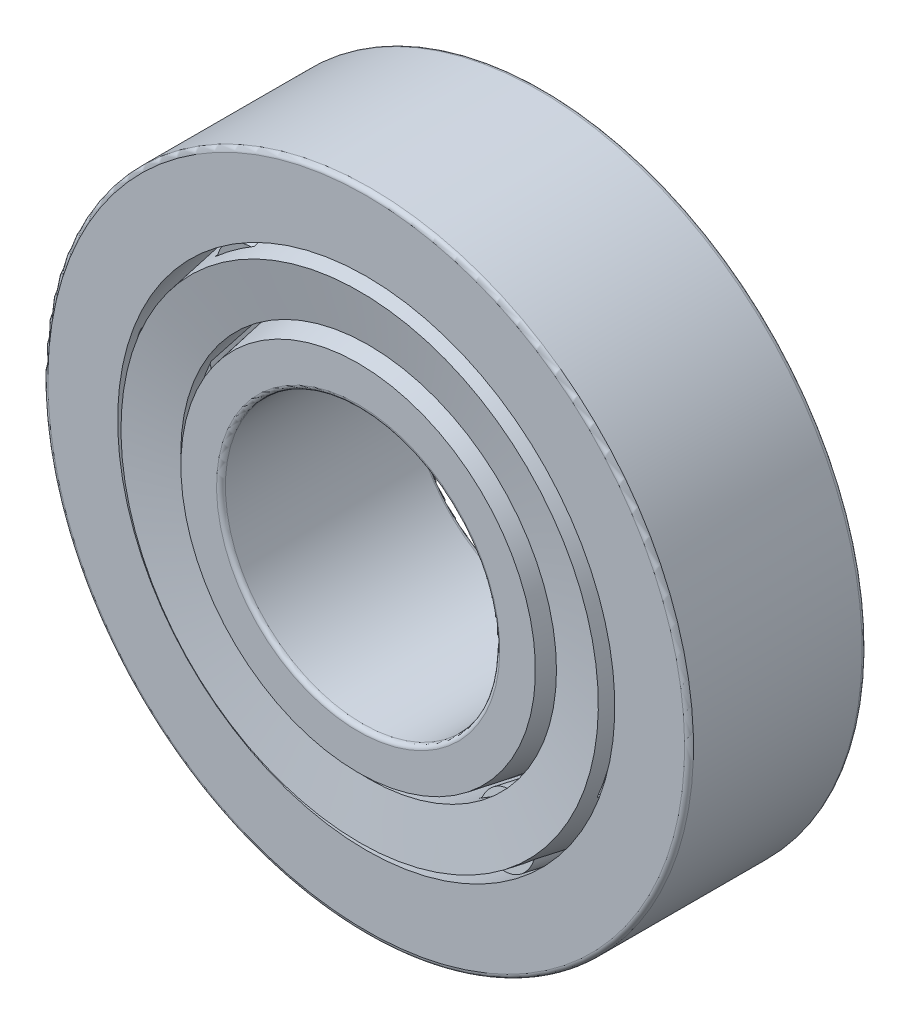
SolidWorks part; units mm, degrees
ref_plane "Front Plane" through (0, 0, 0) normal (0, 0, 1) x (1, 0, 0)
ref_plane "Top Plane" through (0, 0, 0) normal (0, 1, 0) x (1, 0, 0)
ref_plane "Right Plane" through (0, 0, 0) normal (1, 0, 0) x (0, 0, -1)
sketch "Sketch1" plane through (0, 0, 0) normal (1, 0, 0) x (0, 0, -1)
  line L0 (-6, 0) -> (6, 0) construction
  line L1 (0, 0) -> (0, 20) construction
  line L2 (-6, 8.5) -> (6, 8.5) construction
  line L3 (6, 8.5) -> (6, 13.1) construction
  line L4 (6, 13.1) -> (-6, 10.9841) construction
  line L5 (-6, 10.9841) -> (-6, 8.5) construction
  line L7 (-5.5, 20) -> (5.5, 20)
  line L8 (5.5, 20) -> (5.5, 17.3396)
  line L9 (5.5, 17.3396) -> (-5.5, 15.4)
  line L10 (-5.5, 15.4) -> (-5.5, 20)
  line L12 (6.5099, 17.5177) -> (7.25, 13.3204) construction
  line L13 (-5.2599, 11.1146) -> (-6, 15.3118) construction
  line L14 (-6, 10.9841) -> (-5.2599, 11.1146) construction
  line L15 (-6, 10.9841) -> (7.25, 13.3204) construction
  line L20 (-6, -10.9841) -> (7.25, -13.3204) construction
  line L21 (-6, -10.9841) -> (-5.2599, -11.1146) construction
  line L22 (-5.2599, -11.1146) -> (-6, -15.3118) construction
  line L23 (6.5099, -17.5177) -> (7.25, -13.3204) construction
  line L24 (-6, -10.9841) -> (-6, -8.5) construction
  line L25 (6, -13.1) -> (-6, -10.9841) construction
  line L26 (6, -8.5) -> (6, -13.1) construction
  line L27 (-6, -8.5) -> (6, -8.5) construction
  line L28 (-5.5, -15.4) -> (-5.5, -20) construction
  line L29 (5.5, -17.3396) -> (-5.5, -15.4) construction
  line L30 (5.5, -20) -> (5.5, -17.3396) construction
  line L31 (-5.5, -20) -> (5.5, -20) construction
  point P5 (0, 8.5)
  point P37 (0, -8.5)
  dimension "Width" = 12
  dimension "OD" = 40
  dimension "Shaft Dia" = 17
  dimension "D1" = 100
  dimension "D2" = 11.5
  dimension "D3" = 4.6
  dimension "Outer Wd" = 11
  dimension "Bearing Wd" = 13.25
revolve "Revolve1" add sketch "Sketch1" angle 360 about L0
sketch "Sketch5" plane through (0, 0, 0) normal (1, 0, 0) x (0, 0, -1)
  line L0 (6, 13.1) -> (-6, 10.9841) construction
  line L1 (6, 13.1) -> (-6, 10.9841)
  line L2 (-6, 10.9841) -> (-6, 8.5)
  line L3 (-6, 8.5) -> (6, 8.5)
  line L4 (6, 8.5) -> (6, 13.1)
revolve "Revolve4" add sketch "Sketch5" angle 360 about L0
sketch "Sketch2" plane through (0, 0, 0) normal (1, 0, 0) x (0, 0, -1)
  line L0 (-5.9075, 14.7872) -> (-5.3524, 11.6392)
  line L1 (5.5, 16.7986) -> (6.6024, 16.993)
  line L2 (-5.3524, 11.6392) -> (5.5, 13.5528)
  line L3 (6.5099, 17.5177) -> (7.25, 13.3204) construction
  line L4 (5.5, 13.5528) -> (5.5, 16.7986) construction
  line L5 (5.5, 16.7986) -> (-5.9075, 14.7872)
  line L6 (5.5, 17.3396) -> (-5.5, 15.4) construction
  line L7 (6, 13.1) -> (-6, 10.9841) construction
  line L8 (-6, 15.3118) -> (5.5, 17.3396) construction
  line L9 (-5.2599, 11.1146) -> (7.25, 13.3204) construction
  line L10 (6.6024, 16.993) -> (7.1575, 13.8451)
  line L11 (-6, 15.3118) -> (-5.9075, 14.7872) construction
  line L12 (5.5, -20) -> (5.5, 20) construction
  line L13 (5.5, 20) -> (5.5, 17.3396) construction
  line L14 (7.1575, 13.8451) -> (5.5, 13.5528)
  line L15 (-5.3524, 11.6392) -> (-5.2599, 11.1146) construction
  line L16 (0, 0) -> (-6, 0) construction
  line L17 (-6, 10.9841) -> (-6, -10.9841) construction
  line L18 (-5.3524, -11.6392) -> (-5.2599, -11.1146) construction
  line L19 (-6, -15.3118) -> (-5.9075, -14.7872) construction
  line L20 (-5.2599, -11.1146) -> (7.25, -13.3204) construction
  line L21 (-6, -15.3118) -> (5.5, -17.3396) construction
  line L22 (5.5, -13.5528) -> (5.5, -16.7986) construction
  line L23 (7.1575, -13.8451) -> (5.5, -13.5528) construction
  line L24 (6.6024, -16.993) -> (7.1575, -13.8451) construction
  line L25 (5.5, -16.7986) -> (-5.9075, -14.7872) construction
  line L26 (-5.3524, -11.6392) -> (5.5, -13.5528) construction
  line L27 (5.5, -16.7986) -> (6.6024, -16.993) construction
  line L28 (-5.9075, -14.7872) -> (-5.3524, -11.6392) construction
  dimension "D2" = 3.1965
  dimension "D1" = 4.262
revolve "Revolve2" add sketch "Sketch2" angle 360 about L0
sketch "Sketch3" plane through (0, 0, 0) normal (1, 0, 0) x (0, 0, -1)
  line L0 (-5.63, 13.2132) -> (5.5, 15.1757) construction
  line L1 (-5.9075, 14.7872) -> (-5.3524, 11.6392) construction
  line L2 (5.5, 13.5528) -> (5.5, 16.7986) construction
  line L3 (5.5, 17.3396) -> (-5.5, 15.4) construction
  line L4 (-5, 15.4882) -> (-4.63, 13.3895)
  line L5 (-5, 15.4882) -> (5.13, 17.2743)
  line L6 (5.13, 17.2743) -> (5.5, 15.1757)
  line L8 (-4.63, 13.3895) -> (5.5, 15.1757)
  line L9 (-6, 15.3118) -> (-5.5, 15.4) construction
  line L10 (-5.5, 15.4) -> (-5, 15.4882) construction
  line L11 (-5.63, 13.2132) -> (-5.5, 13.2361) construction
  line L12 (-5.5, 20) -> (-5.5, -20) construction
  line L13 (-5.63, 13.2132) -> (-5.5, 13.2361) construction
revolve "Cut-Revolve1" cut sketch "Sketch3" angle 360 about L0
sketch "Sketch4" plane through (0, 0, 0) normal (1, 0, 0) x (0, 0, -1)
  line L0 (-4.9779, 15.3631) -> (5.152, 17.1493)
  line L1 (5.152, 17.1493) -> (5.5, 15.1757)
  line L2 (5.5, 15.1757) -> (-4.63, 13.3895)
  line L3 (-4.63, 13.3895) -> (-5.63, 13.2132) construction
  line L4 (-4.63, 13.3895) -> (-4.9779, 15.3631)
  line L5 (-5.63, 13.2132) -> (-4.63, 13.3895) construction
  line L7 (5.5, 17.3396) -> (-5.5, 15.4) construction
  line L8 (0, 0) -> (-6, 0) construction
  line L9 (-6, 0) -> (6, 0) construction
  line L10 (-5.63, -13.2132) -> (-4.63, -13.3895) construction
  line L11 (-4.63, -13.3895) -> (-5.63, -13.2132) construction
  line L12 (-4.63, -13.3895) -> (-4.9779, -15.3631) construction
  line L13 (5.5, -15.1757) -> (-4.63, -13.3895) construction
  line L14 (5.152, -17.1493) -> (5.5, -15.1757) construction
  line L15 (-4.9779, -15.3631) -> (5.152, -17.1493) construction
  line L17 (-5, 15.4882) -> (-4.63, 13.3895) construction
  dimension "D1" = 0.127
revolve "Revolve3" add sketch "Sketch4" angle 360 about L0
ref_axis "Axis1" through (0, 0, -6) along (0, 0, 1)
pattern_circular "CirPattern1" count 10 every 36 about axis through (0, 0, 0) along (0, 0, 1) of "Cut-Revolve1"
pattern_circular "CirPattern2" count 10 every 36 about axis through (0, 0, -6) along (0, 0, 1) of bodies 403
fillet "Fillet1" radius 0.275 2 edges at (0, -20, -5.5) (0, -20, 5.5)
fillet "Fillet2" radius 0.275 2 edges at (0, -8.5, -6) (0, -8.5, 6)
sketch "Sketch6" plane through (0, 0, 0) normal (1, 0, 0) x (0, 0, -1)
  line L0 (-37, 20) -> (-37, 15.4)
  line L1 (-37, 15.4) -> (-26, 17.3396)
  line L2 (-26, 17.3396) -> (-26, 20)
  line L3 (-26, 20) -> (-37, 20)
  line L4 (-5.5, 20) -> (5.5, 20) construction
  line L5 (5.5, 20) -> (5.5, 17.3396) construction
  line L6 (5.5, 17.3396) -> (-5.5, 15.4) construction
  line L7 (-6, 10.9841) -> (-6, -10.9841) construction
  dimension "D1" = 20
revolve "Revolve5" [suppressed] add sketch "Sketch6" angle 360 about L0
fillet "Fillet3" [suppressed] radius 0.275
delete or keep bodies "Body-Delete1" [suppressed] type delete bodies bodies 399
equation "\"D3@Sketch1\" = \"D2@Sketch1\"/2.5"
equation "\"D2@Sketch2\" = \"D1@Sketch2\"*.75"
equation "\"Rollers@CirPattern2\" = \"OD@Sketch1\"*.24"
equation "\"Angle@CirPattern2\" = 360/\"Rollers@CirPattern2\""
equation "\"D1@CirPattern1\" = \"Rollers@CirPattern2\""
equation "\"D2@CirPattern1\" = \"Angle@CirPattern2\""
equation "\"D1@Fillet1\" = \"Outer Wd@Sketch1\"*.025"
equation "\"D1@Fillet2\" = \"D1@Fillet1\""
equation "\"D1@Fillet3\" = \"D1@Fillet1\""
